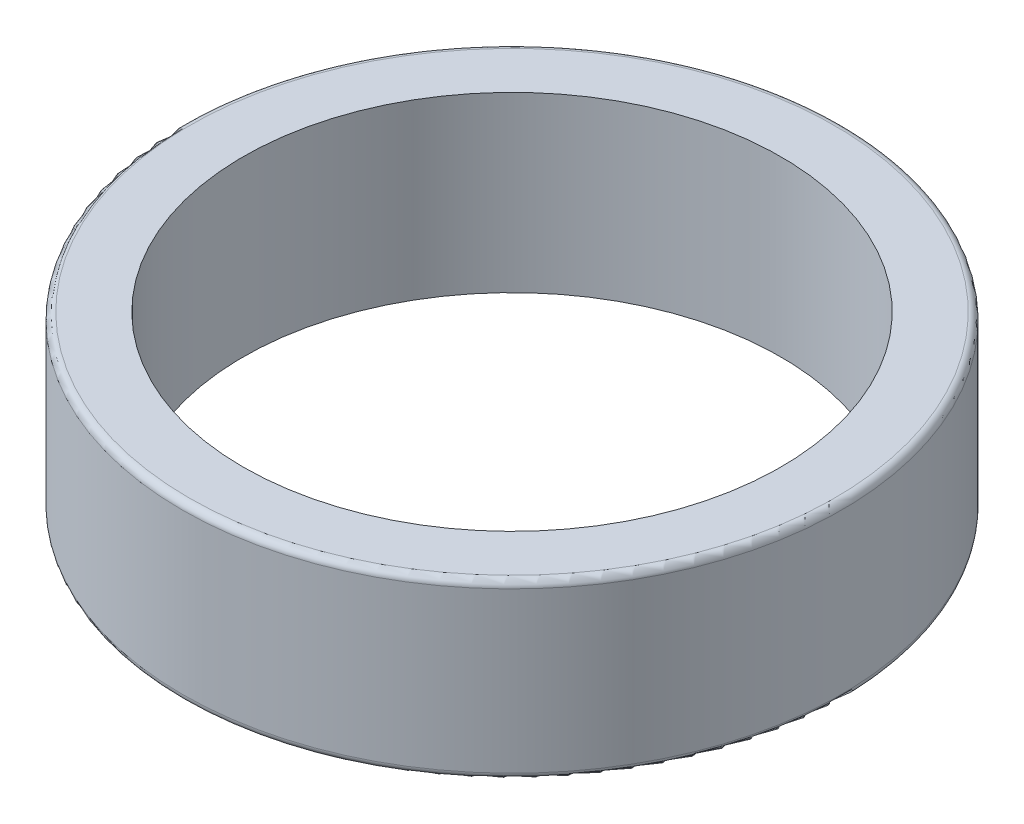
SolidWorks part; units mm, degrees
ref_plane "Front Plane" through (0, 0, 0) normal (0, 0, 1) x (1, 0, 0)
ref_plane "Top Plane" through (0, 0, 0) normal (0, 1, 0) x (1, 0, 0)
ref_plane "Right Plane" through (0, 0, 0) normal (1, 0, 0) x (0, 0, -1)
sketch "Sketch1" plane through (0, 0, 0) normal (0, 1, 0) x (1, 0, 0)
  circle A0 centre (0, 0) radius 9.5
  circle A1 centre (0, 0) radius 7.75
  dimension "D1" = 19
  dimension "D2" = 15.5
extrude "Boss-Extrude1" add sketch "Sketch1" along normal blind 5
fillet "Fillet1" radius 0.2 2 edges at (0, 0, 9.5) (0, 5, 9.5)
